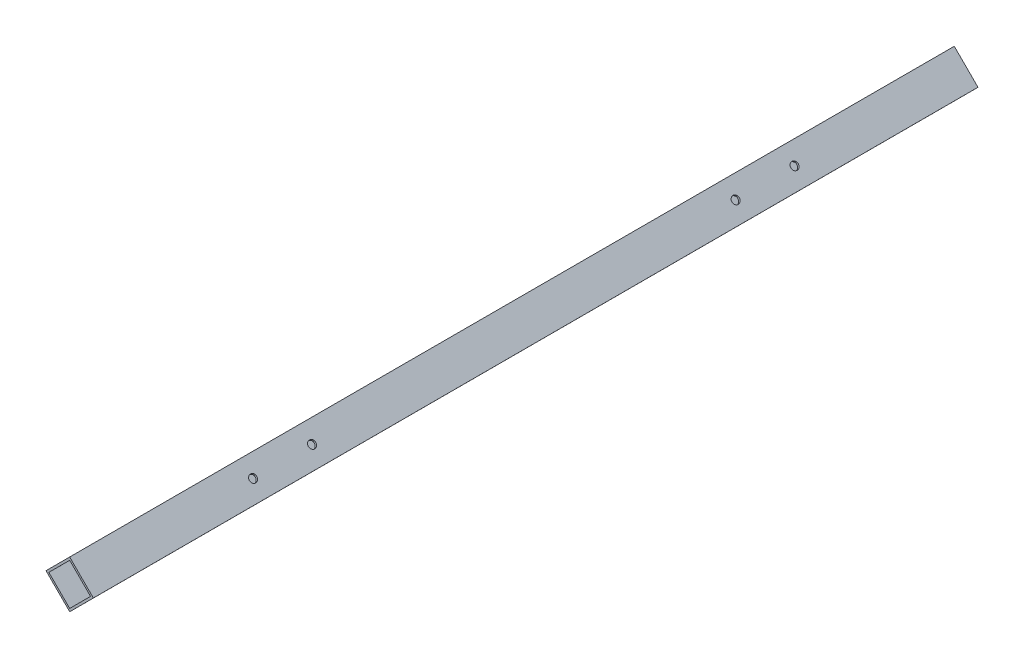
SolidWorks part; units mm, degrees
material "可鍛鑄鐵"
ref_plane "前基準面" through (0, 0, 0) normal (0, 0, 1) x (1, 0, 0)
ref_plane "上基準面" through (0, 0, 0) normal (0, 1, 0) x (1, 0, 0)
ref_plane "右基準面" through (0, 0, 0) normal (1, 0, 0) x (0, 0, -1)
sketch "草圖1" plane through (0, 0, 0) normal (0, 0, 1) x (1, 0, 0)
  line L0 (0, 0) -> (17.6938, -17.6615)
  line L1 (0, 0) -> (-17.6615, -17.6938)
  line L2 (17.6938, -17.6615) -> (0.0323, -35.3553)
  line L3 (-17.6615, -17.6938) -> (0.0323, -35.3553)
  line L4 (0.0019, -2.1213) -> (-15.5402, -17.6919)
  line L5 (0.0019, -2.1213) -> (15.5725, -17.6635)
  line L6 (-15.5402, -17.6919) -> (0.0303, -33.234)
  line L7 (15.5725, -17.6635) -> (0.0303, -33.234)
  point P0 (8.8469, -8.8308)
  dimension "D1" = 25
  dimension "D2" = 25
  dimension "D3" = 1.5
  dimension "D4" = 1.5
  dimension "D5" = 1.5
  dimension "D6" = 1.5
extrude "填料-伸長1" add sketch "草圖1" along normal blind 660
sketch "草圖2" plane through (0, 0, 0) normal (0.7065, 0.7078, 0) x (0.7078, -0.7065, 0)
  line L0 (25, -660) -> (0, -660) construction
  line L1 (25, -660) -> (25, 0) construction
  line L2 (25, 0) -> (0, 0) construction
  line L3 (0, -660) -> (0, 0) construction
  circle A0 centre (12.5, -488) radius 2.75
  circle A1 centre (12.5, -532) radius 2.75
  circle A2 centre (12.5, -128) radius 2.75
  circle A3 centre (12.5, -172) radius 2.75
  dimension "D1" = 5.5
  dimension "D2" = 5.5
  dimension "D4" = 128
  dimension "D5" = 12.5
  dimension "D6" = 12.5
  dimension "D7" = 5.5
  dimension "D8" = 5.5
  dimension "D9" = 44
  dimension "D10" = 128
  dimension "D11" = 12.5
  dimension "D3" = 44
extrude "除料-伸長1" cut sketch "草圖2" against normal through all
